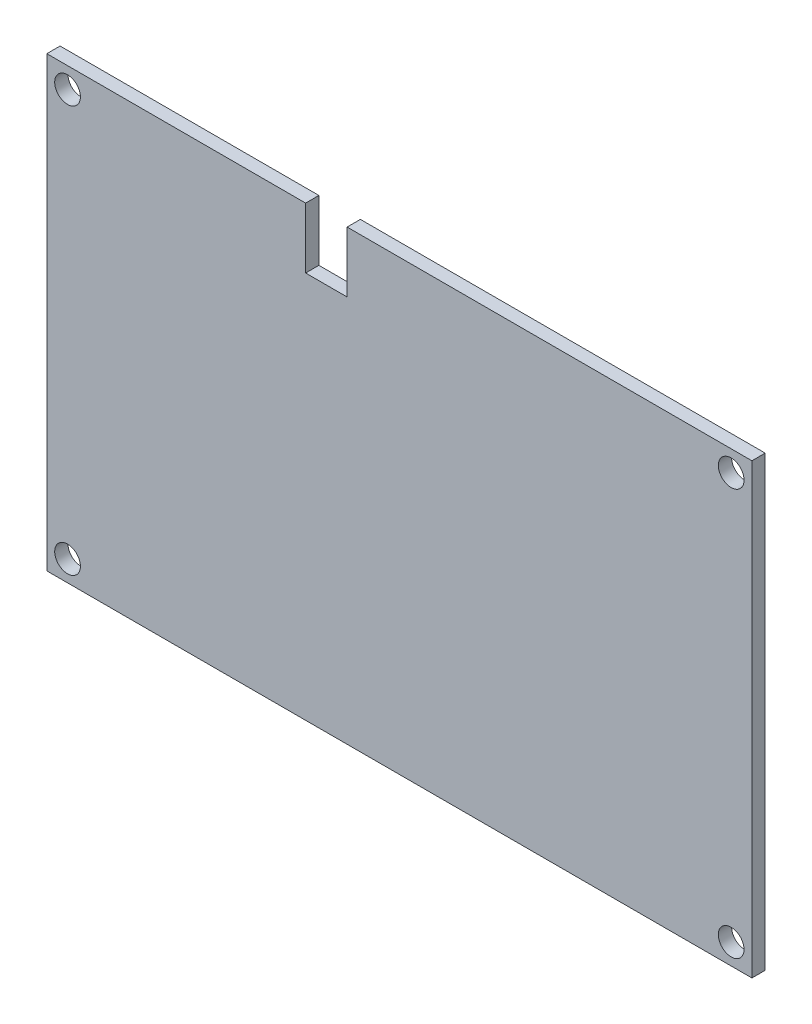
SolidWorks part; units mm, degrees
ref_plane "Спереди" through (0, 0, 0) normal (0, 0, 1) x (1, 0, 0)
ref_plane "Сверху" through (0, 0, 0) normal (0, 1, 0) x (1, 0, 0)
ref_plane "Справа" through (0, 0, 0) normal (1, 0, 0) x (0, 0, -1)
sketch "Эскиз1" plane through (0, 0, 0) normal (0, 0, 1) x (1, 0, 0)
  line L0 (0, 54) -> (31.2, 54)
  line L1 (0, 0) -> (85, 0)
  line L2 (0, 0) -> (0, 54)
  line L3 (31.2, 54) -> (31.2, 46.7)
  line L4 (85, 0) -> (85, 54)
  line L5 (31.2, 46.7) -> (36.2, 46.7)
  line L6 (36.2, 46.7) -> (36.2, 54)
  line L7 (36.2, 54) -> (85, 54)
  circle A0 centre (2.5, 51.5) radius 1.55
  circle A1 centre (82.5, 51.5) radius 1.55
  circle A2 centre (82.5, 2.5) radius 1.55
  circle A3 centre (2.5, 2.5) radius 1.55
  dimension "D6" = 2.5
  dimension "D8" = 2.5
  dimension "D9" = 2.5
  dimension "D10" = 3.1
  dimension "D1" = 5
  dimension "D2" = 7.3
  dimension "D3" = 85
  dimension "D4" = 54
  dimension "D5" = 31.2
  dimension "D7" = 2.5
extrude "Бобышка-Вытянуть1" add sketch "Эскиз1" along normal blind 1.6
